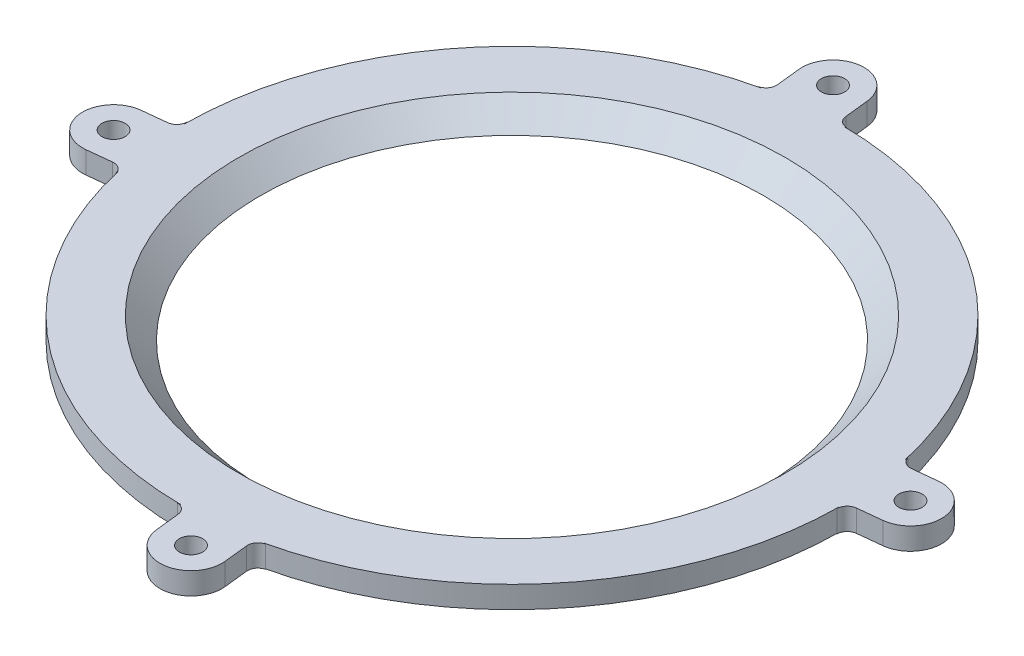
SolidWorks part; units mm, degrees
ref_plane "Front Plane" through (0, 0, 0) normal (0, 0, 1) x (1, 0, 0)
ref_plane "Top Plane" through (0, 0, 0) normal (0, 1, 0) x (1, 0, 0)
ref_plane "Right Plane" through (0, 0, 0) normal (1, 0, 0) x (0, 0, -1)
sketch "Sketch2" plane through (0, 0, 0) normal (1, 0, 0) x (0, 0, -1)
  line L5 (10.1, 0) -> (10.1, 6.9711)
  line L6 (10.1, 6.9711) -> (62.23, 59.1011)
  line L8 (64.3011, 54.1011) -> (15.1, 4.9)
  line L10 (62.23, 59.1011) -> (75, 59.1011)
  line L13 (0, 0) -> (0, 130.9762) construction
  line L14 (75, 59.1011) -> (75, 54.1011)
  line L15 (75, 54.1011) -> (64.3011, 54.1011)
  line L16 (15.1, 4.9) -> (20, 0)
  line L17 (20, 0) -> (10.1, 0)
  dimension "D1" = 5
  dimension "D2" = 75
  dimension "D3" = 10.1
  dimension "D4" = 20
  dimension "D5" = 45
  dimension "D6" = 5
  dimension "D9" = 5
  dimension "D10" = 45
  dimension "D11" = 62.23
revolve "Revolve1" add sketch "Sketch2" angle 360 about L13
fillet "Fillet1" radius 2 1 edges at (0, 4.9, -15.1)
fillet "Fillet2" radius 6 1 edges at (0, 6.9711, -10.1)
scale "Scale1" scale about centroid uniform scaling yes scale factor 0.85
sketch "Sketch4" plane through (0, 6.0324, 0) normal (0, -1, 0) x (1, 0, 0)
  circle A0 centre (0, 0) radius 10.6
  dimension "D1" = 21.2
extrude "Cut-Extrude2" cut sketch "Sketch4" against normal through all
sketch "Sketch9" plane through (0, 52.0183, 0) normal (0, -1, 0) x (1, 0, 0)
  line L0 (-62.1545, 14.4927) -> (-63.8149, -0.9321)
  line L1 (-0.9321, 63.8149) -> (14.4927, 62.1545)
  line L2 (63.8149, 0.9321) -> (62.1545, -14.4927)
  line L3 (-14.4927, -62.1545) -> (0.9321, -63.8149)
  line L8 (64.3163, -12.9583) -> (68.9557, -13.4577)
  line L9 (70.2401, -1.5267) -> (65.6007, -1.0272)
  line L10 (12.9583, 64.3163) -> (13.4577, 68.9557)
  line L11 (1.5267, 70.2401) -> (1.0272, 65.6007)
  line L12 (-64.3163, 12.9583) -> (-68.9557, 13.4577)
  line L13 (-70.2401, 1.5267) -> (-65.6007, 1.0272)
  line L14 (-12.9583, -64.3163) -> (-13.4577, -68.9557)
  line L15 (-1.5267, -70.2401) -> (-1.0272, -65.6007)
  line L16 (64.3163, -12.9583) -> (68.9557, -13.4577)
  line L17 (70.2401, -1.5267) -> (65.6007, -1.0272)
  line L18 (12.9583, 64.3163) -> (13.4577, 68.9557)
  line L19 (1.5267, 70.2401) -> (1.0272, 65.6007)
  line L20 (-64.3163, 12.9583) -> (-68.9557, 13.4577)
  line L21 (-70.2401, 1.5267) -> (-65.6007, 1.0272)
  line L22 (-12.9583, -64.3163) -> (-13.4577, -68.9557)
  line L23 (-1.5267, -70.2401) -> (-1.0272, -65.6007)
  circle A0 centre (-69.5979, 7.4922) radius 2.25 construction
  circle A1 centre (-7.4922, -69.5979) radius 2.25 construction
  circle A2 centre (69.5979, -7.4922) radius 2.25 construction
  circle A3 centre (7.4922, 69.5979) radius 2.25 construction
  circle A4 centre (-69.5979, 7.4922) radius 2.25
  circle A5 centre (-7.4922, -69.5979) radius 2.25
  circle A6 centre (69.5979, -7.4922) radius 2.25
  circle A7 centre (7.4922, 69.5979) radius 2.25
  arc A16 (0.9321, -63.8149) -> (62.1545, -14.4927) centre (0, 0) ccw
  arc A17 (64.3163, -12.9583) -> (62.1545, -14.4927) centre (64.1022, -14.9468) ccw
  arc A18 (68.9557, -13.4577) -> (70.2401, -1.5267) centre (69.5979, -7.4922) ccw
  arc A19 (63.8149, 0.9321) -> (65.6007, -1.0272) centre (65.8147, 0.9613) ccw
  arc A20 (63.8149, 0.9321) -> (14.4927, 62.1545) centre (0, 0) ccw
  arc A21 (12.9583, 64.3163) -> (14.4927, 62.1545) centre (14.9468, 64.1022) ccw
  arc A22 (13.4577, 68.9557) -> (1.5267, 70.2401) centre (7.4922, 69.5979) ccw
  arc A23 (-0.9321, 63.8149) -> (1.0272, 65.6007) centre (-0.9613, 65.8147) ccw
  arc A24 (-0.9321, 63.8149) -> (-62.1545, 14.4927) centre (0, 0) ccw
  arc A25 (-64.3163, 12.9583) -> (-62.1545, 14.4927) centre (-64.1022, 14.9468) ccw
  arc A26 (-68.9557, 13.4577) -> (-70.2401, 1.5267) centre (-69.5979, 7.4922) ccw
  arc A27 (-63.8149, -0.9321) -> (-65.6007, 1.0272) centre (-65.8147, -0.9613) ccw
  arc A28 (-63.8149, -0.9321) -> (-14.4927, -62.1545) centre (0, 0) ccw
  arc A29 (-12.9583, -64.3163) -> (-14.4927, -62.1545) centre (-14.9468, -64.1022) ccw
  arc A30 (-13.4577, -68.9557) -> (-1.5267, -70.2401) centre (-7.4922, -69.5979) ccw
  arc A31 (0.9321, -63.8149) -> (-1.0272, -65.6007) centre (0.9613, -65.8147) ccw
  arc A33 (64.3163, -12.9583) -> (62.1545, -14.4927) centre (64.1022, -14.9468) ccw
  arc A34 (68.9557, -13.4577) -> (70.2401, -1.5267) centre (69.5979, -7.4922) ccw
  arc A35 (63.8149, 0.9321) -> (65.6007, -1.0272) centre (65.8147, 0.9613) ccw
  arc A37 (12.9583, 64.3163) -> (14.4927, 62.1545) centre (14.9468, 64.1022) ccw
  arc A38 (13.4577, 68.9557) -> (1.5267, 70.2401) centre (7.4922, 69.5979) ccw
  arc A39 (-0.9321, 63.8149) -> (1.0272, 65.6007) centre (-0.9613, 65.8147) ccw
  arc A41 (-64.3163, 12.9583) -> (-62.1545, 14.4927) centre (-64.1022, 14.9468) ccw
  arc A42 (-68.9557, 13.4577) -> (-70.2401, 1.5267) centre (-69.5979, 7.4922) ccw
  arc A43 (-63.8149, -0.9321) -> (-65.6007, 1.0272) centre (-65.8147, -0.9613) ccw
  arc A45 (-12.9583, -64.3163) -> (-14.4927, -62.1545) centre (-14.9468, -64.1022) ccw
  arc A46 (-13.4577, -68.9557) -> (-1.5267, -70.2401) centre (-7.4922, -69.5979) ccw
  arc A47 (0.9321, -63.8149) -> (-1.0272, -65.6007) centre (0.9613, -65.8147) ccw
  dimension "D1" = 0
extrude "Boss-Extrude1" add sketch "Sketch9" against normal up to surface (4.25 mm away) up to face at (0, 56.2683, -52.8955)
fillet "Fillet4" radius 3 2 edges at (0, 13.9728, 10.6) (0, 52.0183, -54.6559)
sketch "Sketch11" plane through (0, 52.0183, 0) normal (0, -1, 0) x (1, 0, 0)
  line L16 (-62.2202, 13.8819) -> (-62.1545, 14.4927)
  line L17 (-64.3163, 12.9583) -> (-68.9557, 13.4577)
  line L18 (-70.2401, 1.5267) -> (-65.6007, 1.0272)
  line L19 (-63.8149, -0.9321) -> (-63.7492, -0.3213)
  line L20 (-13.8819, -62.2202) -> (-14.4927, -62.1545)
  line L21 (-12.9583, -64.3163) -> (-13.4577, -68.9557)
  line L22 (-1.5267, -70.2401) -> (-1.0272, -65.6007)
  line L23 (0.9321, -63.8149) -> (0.3213, -63.7492)
  line L24 (62.2202, -13.8819) -> (62.1545, -14.4927)
  line L25 (64.3163, -12.9583) -> (68.9557, -13.4577)
  line L26 (70.2401, -1.5267) -> (65.6007, -1.0272)
  line L27 (63.8149, 0.9321) -> (63.7492, 0.3213)
  line L28 (13.8819, 62.2202) -> (14.4927, 62.1545)
  line L29 (12.9583, 64.3163) -> (13.4577, 68.9557)
  line L30 (1.5267, 70.2401) -> (1.0272, 65.6007)
  line L31 (-0.9321, 63.8149) -> (-0.3213, 63.7492)
  line L32 (-62.2202, 13.8819) -> (-62.1545, 14.4927)
  line L33 (-64.3163, 12.9583) -> (-68.9557, 13.4577)
  line L34 (-70.2401, 1.5267) -> (-65.6007, 1.0272)
  line L35 (-63.8149, -0.9321) -> (-63.7492, -0.3213)
  line L36 (-13.8819, -62.2202) -> (-14.4927, -62.1545)
  line L37 (-12.9583, -64.3163) -> (-13.4577, -68.9557)
  line L38 (-1.5267, -70.2401) -> (-1.0272, -65.6007)
  line L39 (0.9321, -63.8149) -> (0.3213, -63.7492)
  line L40 (62.2202, -13.8819) -> (62.1545, -14.4927)
  line L41 (64.3163, -12.9583) -> (68.9557, -13.4577)
  line L42 (70.2401, -1.5267) -> (65.6007, -1.0272)
  line L43 (63.8149, 0.9321) -> (63.7492, 0.3213)
  line L44 (13.8819, 62.2202) -> (14.4927, 62.1545)
  line L45 (12.9583, 64.3163) -> (13.4577, 68.9557)
  line L46 (1.5267, 70.2401) -> (1.0272, 65.6007)
  line L47 (-0.9321, 63.8149) -> (-0.3213, 63.7492)
  arc A16 (-0.3213, 63.7492) -> (-62.2202, 13.8819) centre (0, 0) ccw
  arc A17 (-64.3163, 12.9583) -> (-62.1545, 14.4927) centre (-64.1022, 14.9468) ccw
  arc A18 (-68.9557, 13.4577) -> (-70.2401, 1.5267) centre (-69.5979, 7.4922) ccw
  arc A19 (-63.8149, -0.9321) -> (-65.6007, 1.0272) centre (-65.8147, -0.9613) ccw
  arc A20 (-63.7492, -0.3213) -> (-13.8819, -62.2202) centre (0, 0) ccw
  arc A21 (-12.9583, -64.3163) -> (-14.4927, -62.1545) centre (-14.9468, -64.1022) ccw
  arc A22 (-13.4577, -68.9557) -> (-1.5267, -70.2401) centre (-7.4922, -69.5979) ccw
  arc A23 (0.9321, -63.8149) -> (-1.0272, -65.6007) centre (0.9613, -65.8147) ccw
  arc A24 (0.3213, -63.7492) -> (62.2202, -13.8819) centre (0, 0) ccw
  arc A25 (64.3163, -12.9583) -> (62.1545, -14.4927) centre (64.1022, -14.9468) ccw
  arc A26 (68.9557, -13.4577) -> (70.2401, -1.5267) centre (69.5979, -7.4922) ccw
  arc A27 (63.8149, 0.9321) -> (65.6007, -1.0272) centre (65.8147, 0.9613) ccw
  arc A28 (63.7492, 0.3213) -> (13.8819, 62.2202) centre (0, 0) ccw
  arc A29 (12.9583, 64.3163) -> (14.4927, 62.1545) centre (14.9468, 64.1022) ccw
  arc A30 (13.4577, 68.9557) -> (1.5267, 70.2401) centre (7.4922, 69.5979) ccw
  arc A31 (-0.9321, 63.8149) -> (1.0272, 65.6007) centre (-0.9613, 65.8147) ccw
  arc A32 (-0.3213, 63.7492) -> (-62.2202, 13.8819) centre (0, 0) ccw
  arc A33 (-64.3163, 12.9583) -> (-62.1545, 14.4927) centre (-64.1022, 14.9468) ccw
  arc A34 (-68.9557, 13.4577) -> (-70.2401, 1.5267) centre (-69.5979, 7.4922) ccw
  arc A35 (-63.8149, -0.9321) -> (-65.6007, 1.0272) centre (-65.8147, -0.9613) ccw
  arc A36 (-63.7492, -0.3213) -> (-13.8819, -62.2202) centre (0, 0) ccw
  arc A37 (-12.9583, -64.3163) -> (-14.4927, -62.1545) centre (-14.9468, -64.1022) ccw
  arc A38 (-13.4577, -68.9557) -> (-1.5267, -70.2401) centre (-7.4922, -69.5979) ccw
  arc A39 (0.9321, -63.8149) -> (-1.0272, -65.6007) centre (0.9613, -65.8147) ccw
  arc A40 (0.3213, -63.7492) -> (62.2202, -13.8819) centre (0, 0) ccw
  arc A41 (64.3163, -12.9583) -> (62.1545, -14.4927) centre (64.1022, -14.9468) ccw
  arc A42 (68.9557, -13.4577) -> (70.2401, -1.5267) centre (69.5979, -7.4922) ccw
  arc A43 (63.8149, 0.9321) -> (65.6007, -1.0272) centre (65.8147, 0.9613) ccw
  arc A44 (63.7492, 0.3213) -> (13.8819, 62.2202) centre (0, 0) ccw
  arc A45 (12.9583, 64.3163) -> (14.4927, 62.1545) centre (14.9468, 64.1022) ccw
  arc A46 (13.4577, 68.9557) -> (1.5267, 70.2401) centre (7.4922, 69.5979) ccw
  arc A47 (-0.9321, 63.8149) -> (1.0272, 65.6007) centre (-0.9613, 65.8147) ccw
  dimension "D1" = 0
extrude "Cut-Extrude3" cut sketch "Sketch11" along normal through all
